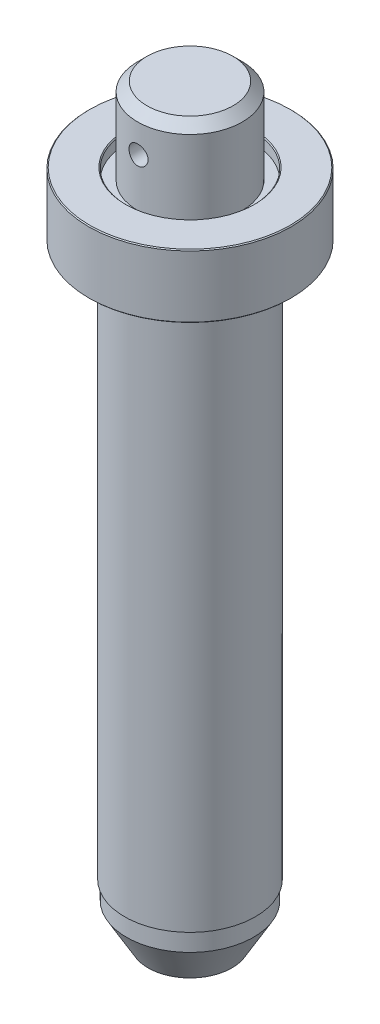
SolidWorks part; units mm, degrees
ref_plane "Front Plane" through (0, 0, 0) normal (0, 0, 1) x (1, 0, 0)
ref_plane "Top Plane" through (0, 0, 0) normal (0, 1, 0) x (1, 0, 0)
ref_plane "Right Plane" through (0, 0, 0) normal (1, 0, 0) x (0, 0, -1)
sketch "Sketch1" plane through (0, 0, 0) normal (0, 0, 1) x (1, 0, 0)
  line L0 (0, 0) -> (0, 200) construction
  line L1 (17.5, 15) -> (17.5, 158)
  line L2 (27.1, 163) -> (27.1, 180)
  line L3 (0, 0) -> (11.2265, 0)
  line L4 (17, 15) -> (17.5, 15)
  line L5 (0, 200) -> (14, 200) construction
  line L6 (0, 200) -> (11.5, 200)
  line L7 (17, 180) -> (27.1, 180)
  line L8 (14, 197.5) -> (11.5, 200)
  line L9 (0, 180) -> (14, 180) construction
  line L10 (14, 177) -> (14, 197.5)
  line L11 (17.5, 0) -> (17.5, 200) construction
  line L12 (22.5, 163) -> (27.1, 163)
  line L13 (27.1, 0) -> (27.1, 200) construction
  line L14 (17, 10) -> (11.2265, 0)
  line L15 (14, 163) -> (27.1, 163) construction
  line L16 (17, 15) -> (17, 10)
  line L17 (0, 0) -> (0, 200)
  line L18 (14, 177) -> (17, 177)
  line L21 (17, 177) -> (17, 180)
  line L22 (14, 180) -> (27.1, 180) construction
  line L23 (14, 177) -> (27.1, 177) construction
  arc A0 (22.5, 163) -> (17.5, 158) centre (22.5, 158) ccw
  point P13 (17, 0)
  point P18 (17, 200)
  point P19 (0, 10)
  point P20 (17.5, 10)
  dimension "D4" = 5
  dimension "D1" = 200
  dimension "D5" = 20
  dimension "D9" = 30
  dimension "D2" = 17.5
  dimension "D3" = 27.1
  dimension "D6" = 17
  dimension "D8" = 3
revolve "Revolve1" add sketch "Sketch1" angle 360 about L17
chamfer "Chamfer1" distance 0.25 angle 45 1 edges at (0, 180, -27.1)
chamfer "Chamfer2" distance 0.25 angle 45 1 edges at (0, 163, -27.1)
chamfer "Chamfer3" distance 0.25 angle 45 1 edges at (0, 180, -17)
sketch "Sketch2" plane through (0, 0, 0) normal (0, 0, 1) x (1, 0, 0)
  circle A0 centre (0, 189.875) radius 2.55
  dimension "D1" = 5.1
extrude "Cut-Extrude1" cut sketch "Sketch2" against normal mid plane 30
